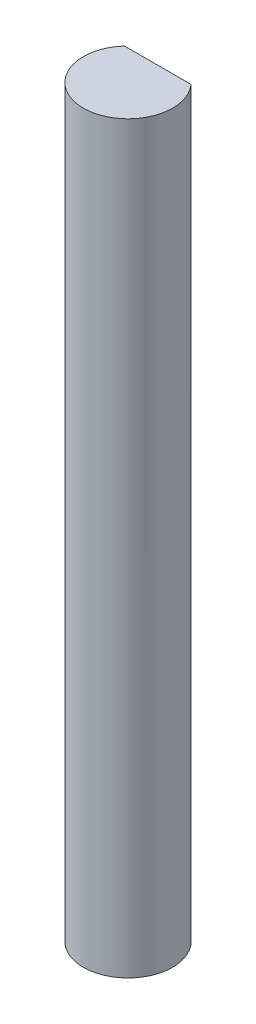
SolidWorks part; units mm, degrees
ref_plane "Front Plane" through (0, 0, 0) normal (0, 0, 1) x (1, 0, 0)
ref_plane "Top Plane" through (0, 0, 0) normal (0, 1, 0) x (1, 0, 0)
ref_plane "Right Plane" through (0, 0, 0) normal (1, 0, 0) x (0, 0, -1)
sketch "Sketch1" plane through (0, 0, 0) normal (0, 1, 0) x (1, 0, 0)
  circle A0 centre (0, 0) radius 3
extrude "Boss-Extrude1" add sketch "Sketch1" along normal blind 50
sketch "Sketch2" plane through (0, 50, 0) normal (0, 1, 0) x (1, 0, 0)
  line L0 (-2.2361, 2) -> (2.2361, 2)
  arc A0 (2.2361, 2) -> (-2.2361, 2) centre (0, 0) ccw
  dimension "D1" = 6
  dimension "D2" = 2
extrude "Cut-Extrude1" cut sketch "Sketch2" against normal blind 12
